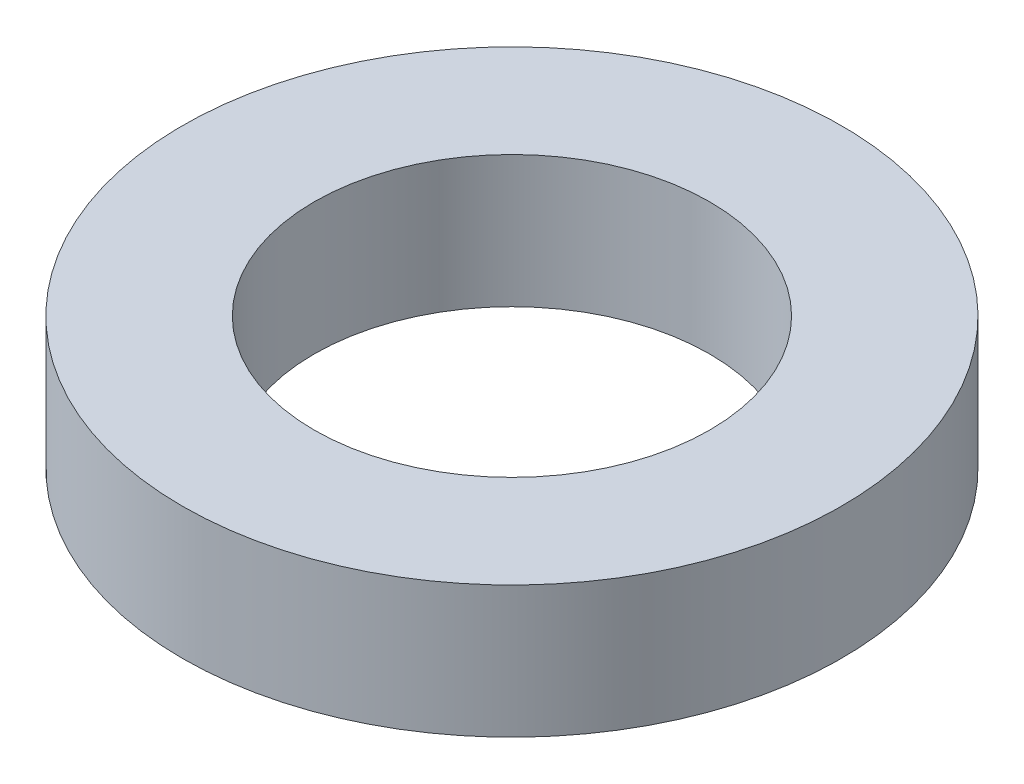
SolidWorks part; units mm, degrees
material "Nylon 6/10"
ref_plane "Front Plane" through (0, 0, 0) normal (0, 0, 1) x (1, 0, 0)
ref_plane "Top Plane" through (0, 0, 0) normal (0, 1, 0) x (1, 0, 0)
ref_plane "Right Plane" through (0, 0, 0) normal (1, 0, 0) x (0, 0, -1)
sketch "Sketch1" plane through (0, 0, 0) normal (0, 1, 0) x (1, 0, 0)
  circle A0 centre (0, 0) radius 1.5
  circle A1 centre (0, 0) radius 2.5
  dimension "D1" = 5
  dimension "D2" = 3
extrude "Boss-Extrude1" add sketch "Sketch1" along normal mid plane 1
